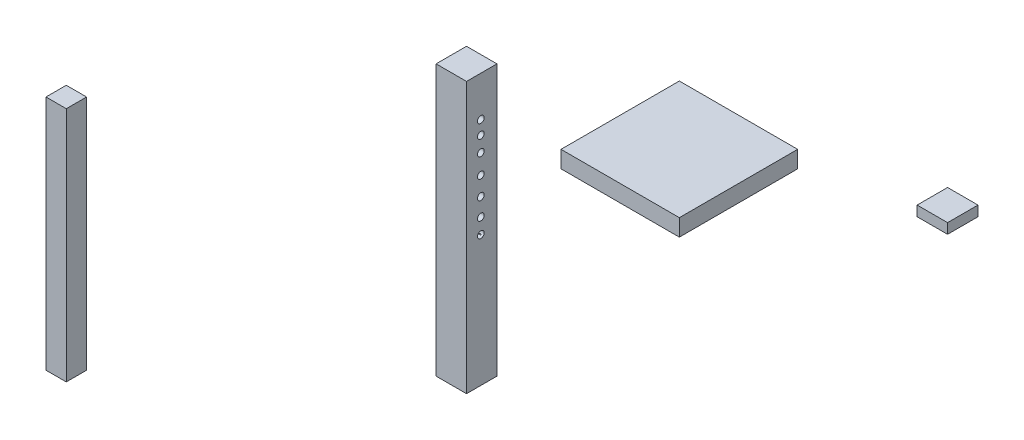
SolidWorks part; units mm, degrees
ref_plane "Front Plane" through (0, 0, 0) normal (0, 0, 1) x (1, 0, 0)
ref_plane "Top Plane" through (0, 0, 0) normal (0, 1, 0) x (1, 0, 0)
ref_plane "Right Plane" through (0, 0, 0) normal (1, 0, 0) x (0, 0, -1)
sketch "Sketch1" plane through (0, 0, 0) normal (0, 1, 0) x (1, 0, 0)
  line L1 (-32.8678, 15.1033) -> (57.1322, 15.1033)
  line L2 (-32.8678, 15.1033) -> (-32.8678, 105.1033)
  line L3 (-32.8678, 105.1033) -> (57.1322, 105.1033)
  line L4 (57.1322, 15.1033) -> (57.1322, 105.1033)
extrude "Boss-Extrude2" add sketch "Sketch1" against normal blind 30
sketch "Sketch2" plane through (0, 0, 0) normal (0, 1, 0) x (1, 0, 0)
  line L1 (-702.2844, -368.8199) -> (-352.2844, -368.8199)
  line L2 (-702.2844, -368.8199) -> (-702.2844, -18.8199)
  line L3 (-702.2844, -18.8199) -> (-352.2844, -18.8199)
  line L4 (-352.2844, -368.8199) -> (-352.2844, -18.8199)
extrude "Boss-Extrude3" add sketch "Sketch2" against normal blind 50 separate body
sketch "Sketch3" plane through (0, 0, 0) normal (0, 1, 0) x (1, 0, 0)
  line L1 (-1105.9976, -334.6086) -> (-1015.9976, -334.6086)
  line L2 (-1105.9976, -334.6086) -> (-1105.9976, -244.6086)
  line L3 (-1105.9976, -244.6086) -> (-1015.9976, -244.6086)
  line L4 (-1015.9976, -334.6086) -> (-1015.9976, -244.6086)
extrude "Boss-Extrude4" add sketch "Sketch3" against normal blind 800 separate body
sketch "Sketch4" plane through (-1015.9976, 0, 0) normal (1, 0, 0) x (0, 0, -1)
  circle A0 centre (-292.2657, -118.793) radius 10
  circle A1 centre (-292.2657, -158.7655) radius 10
  circle A2 centre (-292.2657, -203.7344) radius 10
  circle A3 centre (-292.2657, -261.1947) radius 10
  circle A4 centre (-292.2657, -316.1568) radius 10
  circle A5 centre (-292.2657, -368.6206) radius 10
  circle A6 centre (-292.2657, -413.5895) radius 1
  circle A7 centre (-292.2657, -413.5895) radius 10
sketch "Sketch5" plane through (0, 0, 0) normal (0, 1, 0) x (1, 0, 0)
  line L1 (-1598.0556, -996.3759) -> (-1538.0556, -996.3759)
  line L2 (-1598.0556, -996.3759) -> (-1598.0556, -936.3759)
  line L3 (-1598.0556, -936.3759) -> (-1538.0556, -936.3759)
  line L4 (-1538.0556, -996.3759) -> (-1538.0556, -936.3759)
extrude "Boss-Extrude5" add sketch "Sketch5" against normal blind 700 separate body
extrude "Cut-Extrude2" cut sketch "Sketch4" against normal through all
